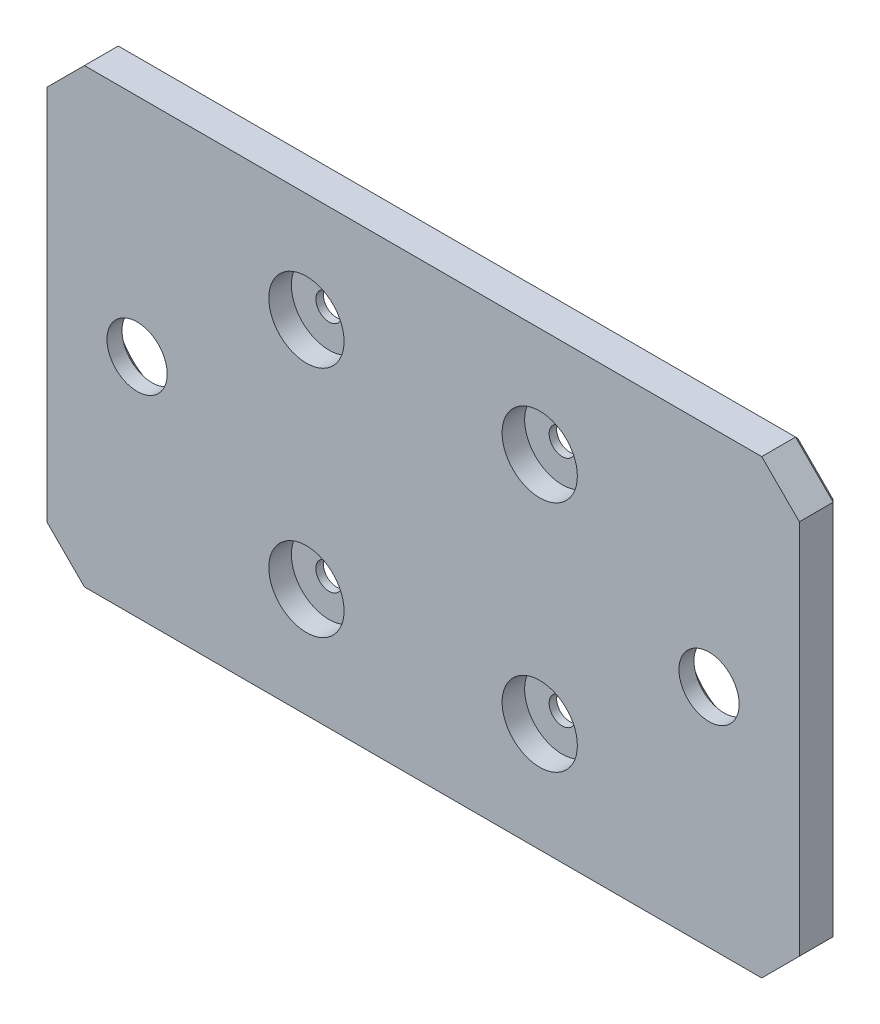
SolidWorks part; units mm, degrees
ref_plane "Płaszczyzna przednia" through (0, 0, 0) normal (0, 0, 1) x (1, 0, 0)
ref_plane "Płaszczyzna górna" through (0, 0, 0) normal (0, 1, 0) x (1, 0, 0)
ref_plane "Płaszczyzna prawa" through (0, 0, 0) normal (1, 0, 0) x (0, 0, -1)
sketch "Sketch1" plane through (0, 0, 0) normal (0, 0, 1) x (1, 0, 0)
  line L1 (-50, -30) -> (50, -30)
  line L2 (-50, -30) -> (-50, 30)
  line L3 (-50, 30) -> (50, 30)
  line L4 (50, -30) -> (50, 30)
  line L5 (-50, -30) -> (50, 30) construction
  line L6 (-50, 30) -> (50, -30) construction
  point P0 (0, 0)
  dimension "D1" = 60
  dimension "D2" = 100
extrude "Boss-Extrude1" add sketch "Sketch1" along normal blind 5
sketch "Sketch3" plane through (0, 0, 0) normal (0, 0, 1) x (1, 0, 0)
  line L1 (21.75, 21.75) -> (-21.75, 21.75)
  line L2 (21.75, 21.75) -> (21.75, -21.75)
  line L3 (21.75, -21.75) -> (-21.75, -21.75)
  line L4 (-21.75, 21.75) -> (-21.75, -21.75)
  line L5 (21.75, 21.75) -> (-21.75, -21.75) construction
  line L6 (21.75, -21.75) -> (-21.75, 21.75) construction
  point P0 (0, 0)
  dimension "D1" = 43.5
  dimension "D2" = 43.5
extrude "Cut-Extrude1" cut sketch "Sketch3" along normal blind 1
sketch "Sketch4" plane through (0, 0, -48) normal (0, 0, 1) x (1, 0, 0)
  circle A0 centre (-15.5, 15.5) radius 1.75
  circle A1 centre (15.5, 15.5) radius 1.75
  circle A2 centre (15.5, -15.5) radius 1.75
  circle A3 centre (-15.5, -15.5) radius 1.75
  dimension "D1" = 3.5
extrude "Cut-Extrude3" cut sketch "Sketch4" along normal blind 92 and the other way blind 1
sketch "Sketch5" plane through (0, 0, 5) normal (0, 0, 1) x (1, 0, 0)
  circle A0 centre (-15.5, 15.5) radius 5
  circle A1 centre (15.5, 15.5) radius 5
  circle A2 centre (15.5, -15.5) radius 5
  circle A3 centre (-15.5, -15.5) radius 5
  dimension "D1" = 10
extrude "Cut-Extrude4" cut sketch "Sketch5" against normal blind 3
sketch "Sketch6" plane through (0, 0, 0) normal (0, 0, -1) x (-1, 0, 0)
  line L0 (-50, 0) -> (50, 0) construction
  line L1 (-50, -30) -> (-50, 30) construction
  line L2 (50, 30) -> (50, -30) construction
  circle A0 centre (-38, 0) radius 4
  circle A1 centre (38, 0) radius 4
  dimension "D1" = 8
  dimension "D2" = 8
  dimension "D3" = 12
  dimension "D4" = 12
extrude "Cut-Extrude5" cut sketch "Sketch6" against normal through all both and the other way through all
sketch "Sketch7" plane through (0, 0, 0) normal (0, 0, -1) x (-1, 0, 0)
  circle A0 centre (-38, 0) radius 7.5
  circle A1 centre (38, 0) radius 7.5
  dimension "D1" = 15
  dimension "D2" = 15
extrude "Cut-Extrude6" cut sketch "Sketch7" against normal blind 3
chamfer "Chamfer1" distance 0.5 angle 45 2 edges at (30.5, 0, 0) (-45.5, 0, 0)
chamfer "Chamfer2" distance 5 angle 45 4 edges at (50, 30, 2.5) (-50, 30, 2.5) (-50, -30, 2.5) (50, -30, 2.5)
chamfer "Chamfer3" distance 0.5 angle 45 8 edges at (-50, 0, 0) (-47.5, 27.5, 0) (0, 30, 0) (47.5, 27.5, 0) (50, 0, 0) (47.5, -27.5, 0) (0, -30, 0) (-47.5, -27.5, 0)
